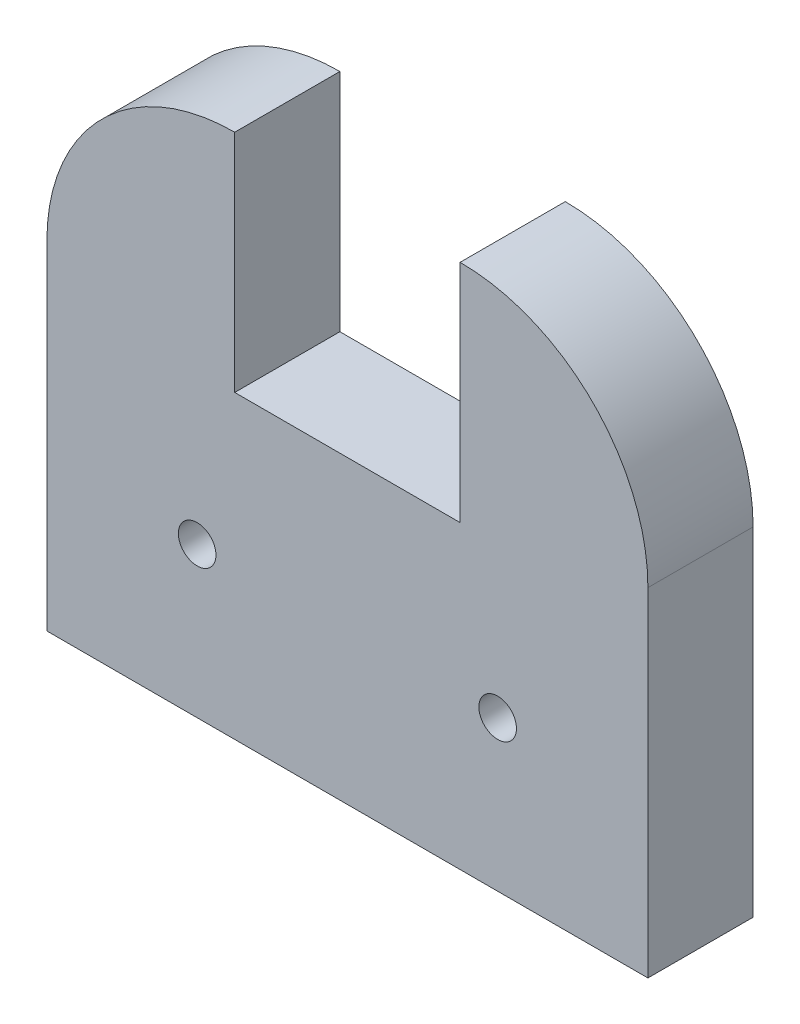
SolidWorks part; units mm, degrees
ref_plane "Front Plane" through (0, 0, 0) normal (0, 0, 1) x (1, 0, 0)
ref_plane "Top Plane" through (0, 0, 0) normal (0, 1, 0) x (1, 0, 0)
ref_plane "Right Plane" through (0, 0, 0) normal (1, 0, 0) x (0, 0, -1)
sketch "Sketch1" plane through (0, 0, 0) normal (0, 0, 1) x (1, 0, 0)
  line L1 (-45.8725, 52.0606) -> (55.7275, 52.0606)
  line L2 (-45.8725, 52.0606) -> (-45.8725, -36.8394)
  line L3 (-45.8725, -36.8394) -> (55.7275, -36.8394)
  line L4 (55.7275, 52.0606) -> (55.7275, -36.8394)
  dimension "D1" = 88.9
  dimension "D2" = 101.6
extrude "Boss-Extrude1" add sketch "Sketch1" along normal blind 17.78
sketch "Sketch2" plane through (0, 0, 17.78) normal (0, 0, 1) x (1, 0, 0)
  line L0 (-45.8725, -36.8394) -> (55.7275, -36.8394) construction
  line L1 (-45.8725, 52.0606) -> (-45.8725, -36.8394) construction
  line L2 (55.7275, -36.8394) -> (55.7275, 52.0606) construction
  circle A0 centre (-20.4725, -11.4394) radius 3.175
  circle A1 centre (30.3275, -11.4394) radius 3.175
  dimension "D1" = 6.35
  dimension "D4" = 6.35
  dimension "D2" = 25.4
  dimension "D3" = 25.4
  dimension "D5" = 25.4
  dimension "D6" = 25.4
extrude "Cut-Extrude1" cut sketch "Sketch2" against normal through all
fillet "Fillet1" radius 31.75 2 edges at (55.7275, 52.0606, 8.89) (-45.8725, 52.0606, 8.89)
sketch "Sketch3" plane through (0, 0, 17.78) normal (0, 0, 1) x (1, 0, 0)
  line L1 (-14.1225, 52.0606) -> (23.9775, 52.0606)
  line L2 (-14.1225, 52.0606) -> (-14.1225, 13.9606)
  line L3 (-14.1225, 13.9606) -> (23.9775, 13.9606)
  line L4 (23.9775, 52.0606) -> (23.9775, 13.9606)
  dimension "D1" = 0
  dimension "D2" = 38.1
extrude "Cut-Extrude2" cut sketch "Sketch3" against normal through all
